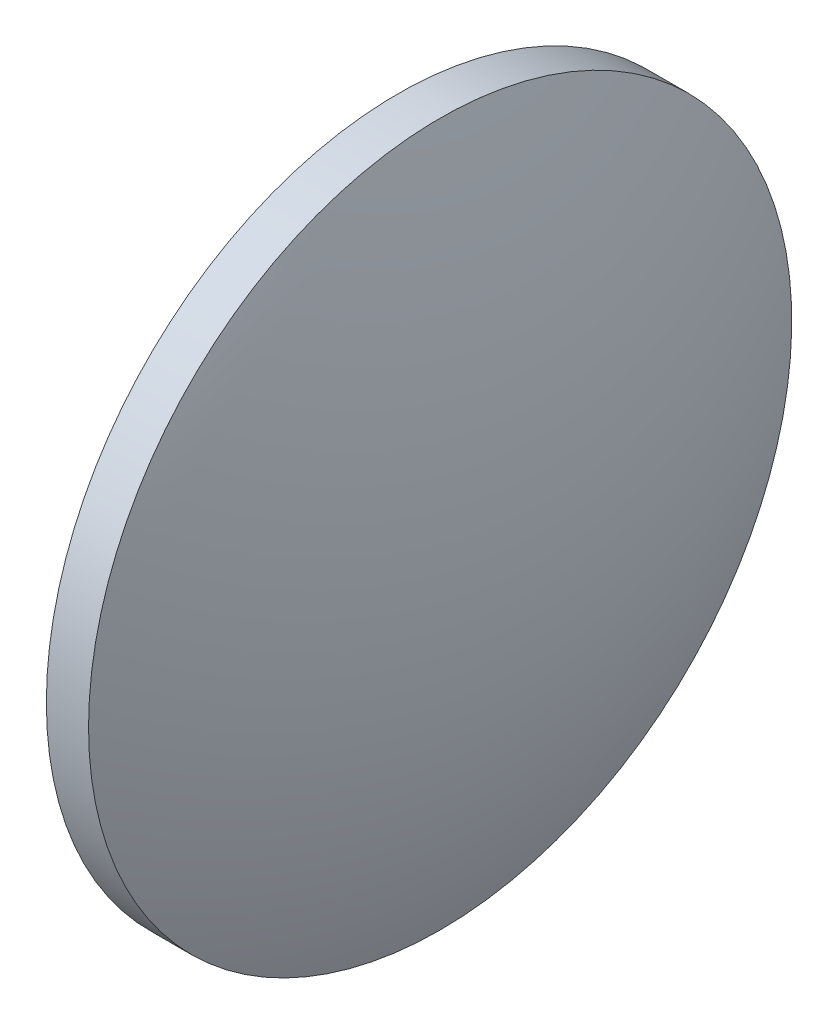
SolidWorks part; units mm, degrees
ref_plane "前视基准面" through (0, 0, 0) normal (0, 0, 1) x (1, 0, 0)
ref_plane "上视基准面" through (0, 0, 0) normal (0, 1, 0) x (1, 0, 0)
ref_plane "右视基准面" through (0, 0, 0) normal (1, 0, 0) x (0, 0, -1)
sketch "草图1" plane through (0, 0, 0) normal (0, 0, 1) x (1, 0, 0)
  line L0 (588.3922, 196.7023) -> (597.9803, 196.7023) construction
  line L1 (590.7579, 196.7023) -> (590.7579, 209.2023)
  line L2 (594.7579, 196.7023) -> (590.7579, 196.7023)
  line L5 (590.7579, 209.2023) -> (592.2579, 209.2023)
  arc A0 (594.7579, 196.7023) -> (592.2579, 209.2023) centre (562.2579, 196.7023) ccw
revolve "旋转1" add sketch "草图1" angle 360 about L0
